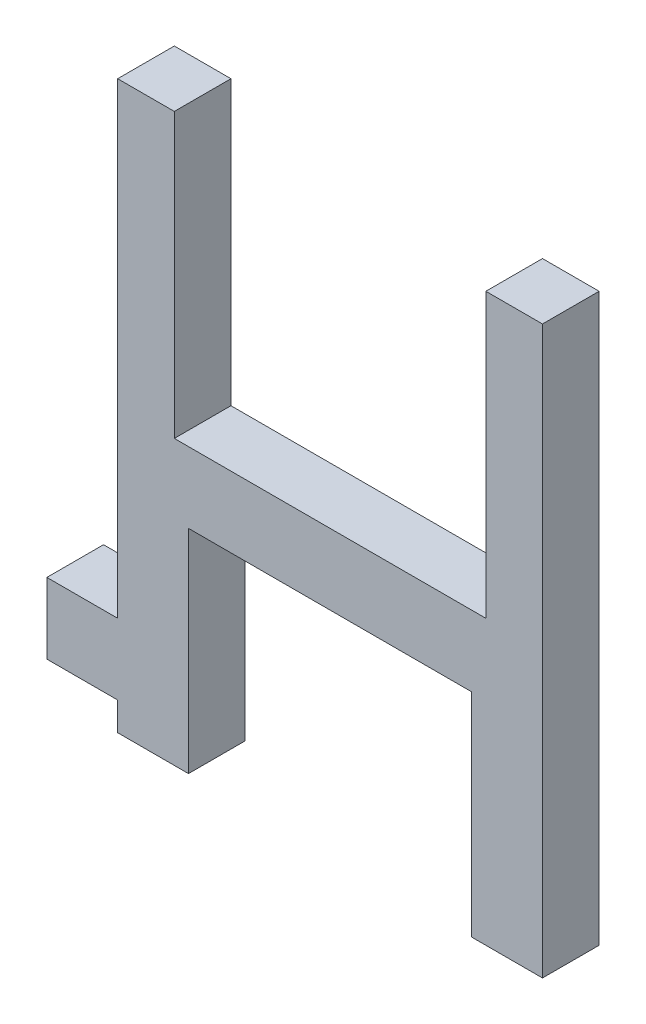
SolidWorks part; units mm, degrees
ref_plane "Přední rovina" through (0, 0, 0) normal (0, 0, 1) x (1, 0, 0)
ref_plane "Horní rovina" through (0, 0, 0) normal (0, 1, 0) x (1, 0, 0)
ref_plane "Pravá rovina" through (0, 0, 0) normal (1, 0, 0) x (0, 0, -1)
sketch "Skica1" plane through (0, 0, 0) normal (0, 0, 1) x (1, 0, 0)
  line L0 (0, 0) -> (5, 0)
  line L1 (5, 0) -> (5, -2)
  line L2 (5, -2) -> (10, -2)
  line L3 (10, -2) -> (10, 4.0825)
  line L4 (10, 4.0825) -> (10, 13)
  line L5 (10, 13) -> (30, 13)
  line L6 (30, 13) -> (30, -2)
  line L7 (30, -2) -> (35, -2)
  line L8 (35, -2) -> (35, 18)
  line L9 (35, 18) -> (5, 18)
  line L10 (5, 18) -> (5, 5)
  line L11 (5, 5) -> (0, 5)
  line L12 (0, 5) -> (0, 0)
  point P3 (2.5, 0)
  dimension "D1" = 5
  dimension "D2" = 20
  dimension "D3" = 5
  dimension "D4" = 15
  dimension "D5" = 5
  dimension "D6" = 6.0825
  dimension "D7" = 2
  dimension "D8" = 5
  dimension "D9" = 5
  dimension "D10" = 20
extrude "Přidat vysunutím1" add sketch "Skica1" along normal blind 4
sketch "Skica2" plane through (0, 18, 0) normal (0, 1, 0) x (1, 0, 0)
  line L0 (35, 0) -> (5, 0) construction
  line L1 (10, 0) -> (30, 0)
  line L2 (10, 0) -> (10, -4)
  line L3 (10, -4) -> (30, -4)
  line L4 (30, 0) -> (30, -4)
  line L5 (35, -4) -> (5, -4) construction
  line L6 (5, -4) -> (5, 0) construction
  line L7 (35, -4) -> (35, 0) construction
  dimension "D1" = 5
  dimension "D2" = 5
extrude "Přidat vysunutím2" add sketch "Skica2" along normal blind 15
sketch "Skica3" plane through (0, 0, 4) normal (0, 0, 1) x (1, 0, 0)
  line L1 (17.25, 29.5) -> (22.75, 29.5)
  line L2 (17.25, 29.5) -> (17.25, 26.5)
  line L3 (17.25, 26.5) -> (22.75, 26.5)
  line L4 (22.75, 29.5) -> (22.75, 26.5)
  line L6 (10, 18) -> (5, 18) construction
  line L7 (10, 33) -> (10, 18) construction
  point P6 (17.25, 28)
  point P7 (0, 0)
  dimension "D1" = 3
  dimension "D2" = 5.5
  dimension "D3" = 8.5
  dimension "D4" = 7.25
extrude "Odebrat vysunutím1" cut sketch "Skica3" against normal blind 15
sketch "Skica4" plane through (0, 0, 4) normal (0, 0, 1) x (1, 0, 0)
  line L1 (10, 33) -> (30, 33)
  line L2 (10, 33) -> (10, 18)
  line L3 (10, 18) -> (30, 18)
  line L4 (30, 33) -> (30, 18)
extrude "Odebrat vysunutím2" cut sketch "Skica4" against normal blind 15
sketch "Skica5" plane through (0, 18, 0) normal (0, 1, 0) x (1, 0, 0)
  line L1 (5, 0) -> (9, 0)
  line L2 (5, 0) -> (5, -4)
  line L3 (5, -4) -> (9, -4)
  line L4 (9, 0) -> (9, -4)
  line L5 (35, -4) -> (5, -4) construction
  line L7 (35, 0) -> (31, 0)
  line L8 (35, 0) -> (35, -4)
  line L9 (35, -4) -> (31, -4)
  line L10 (31, 0) -> (31, -4)
  dimension "D1" = 4
  dimension "D2" = 4
  dimension "D3" = 4
  dimension "D4" = 4
extrude "Přidat vysunutím3" add sketch "Skica5" along normal blind 20
